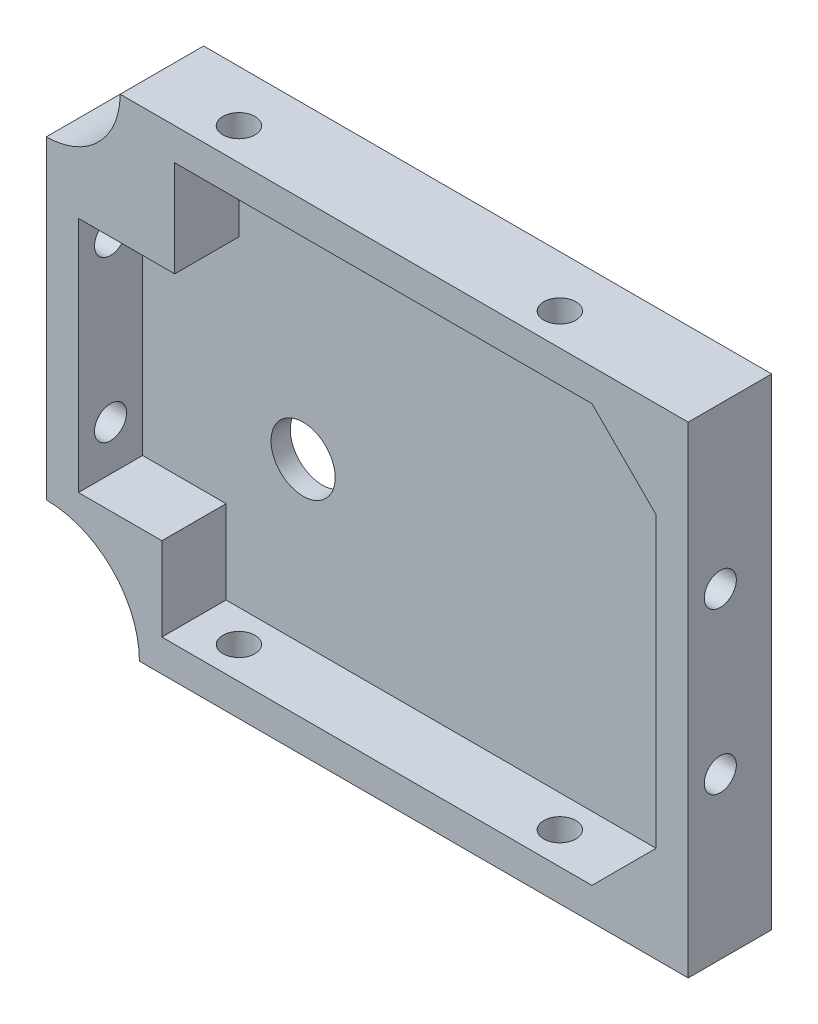
SolidWorks part; units mm, degrees
ref_plane "Plan de face" through (0, 0, 0) normal (0, 0, 1) x (1, 0, 0)
ref_plane "Plan de dessus" through (0, 0, 0) normal (0, 1, 0) x (1, 0, 0)
ref_plane "Plan de droite" through (0, 0, 0) normal (1, 0, 0) x (0, 0, -1)
sketch "Esquisse1" plane through (0, 0, 0) normal (0, 0, 1) x (1, 0, 0)
  line L0 (44.1184, 33.7284) -> (54.1184, 33.7284)
  line L1 (-45.8816, 33.7284) -> (44.1184, 33.7284)
  line L2 (-45.8816, 33.7284) -> (-45.8816, -41.2716)
  line L3 (-45.8816, -41.2716) -> (54.1184, -41.2716)
  line L4 (54.1184, 23.7284) -> (54.1184, -41.2716)
  line L5 (54.1184, 33.7284) -> (54.1184, 23.7284)
  point P6 (54.1184, 33.7284)
  dimension "D1" = 100
  dimension "D2" = 75
extrude "Boss.-Extru.1" add sketch "Esquisse1" along normal blind 13
shell "Coque1" thickness 5
sketch "Esquisse2" plane through (-45.8816, 0, 0) normal (-1, 0, 0) x (0, 0, 1)
  line L0 (13, 33.7284) -> (13, -41.2716) construction
  line L1 (13, 33.7284) -> (0, 33.7284) construction
  line L2 (13, -41.2716) -> (0, -41.2716) construction
  circle A0 centre (8, 8.7284) radius 2.5
  circle A1 centre (8, -16.2716) radius 2.5
  dimension "D1" = 5
  dimension "D2" = 5
  dimension "D3" = 5
  dimension "D4" = 5
  dimension "D5" = 25
  dimension "D6" = 25
extrude "Enlèv. mat.-Extru.1" cut sketch "Esquisse2" against normal up to surface (100 mm away) contours A1 | A0 up to face at (54.1184, -3.7716, 6.5)
sketch "Esquisse3" plane through (0, -41.2716, 0) normal (0, -1, 0) x (1, 0, 0)
  line L0 (-45.8816, 13) -> (54.1184, 13) construction
  line L2 (54.1184, 13) -> (54.1184, 0) construction
  line L3 (-45.8816, 13) -> (-45.8816, 0) construction
  circle A0 centre (-20.8816, 8) radius 2.5
  circle A1 centre (29.1184, 8) radius 2.5
  dimension "D1" = 5
  dimension "D2" = 5
  dimension "D3" = 5
  dimension "D4" = 5
  dimension "D5" = 25
  dimension "D6" = 25
extrude "Enlèv. mat.-Extru.2" cut sketch "Esquisse3" against normal up to surface (75 mm away) up to face at (4.1184, 33.7284, 6.5)
sketch "Esquisse4" plane through (0, 0, 3) normal (0, 0, 1) x (1, 0, 0)
  line L1 (49.1184, 28.7284) -> (-40.8816, 28.7284) construction
  line L2 (-45.8816, -41.2716) -> (-27.8816, -41.2716)
  line L3 (-40.8816, 28.7284) -> (-40.8816, -36.2716) construction
  line L4 (-45.8816, -41.2716) -> (-45.8816, -23.2716)
  line L5 (49.1184, 28.7284) -> (49.1184, 18.7284)
  line L6 (49.1184, -36.2716) -> (49.1184, 28.7284) construction
  line L7 (49.1184, 18.7284) -> (39.1184, 28.7284)
  line L8 (39.1184, 28.7284) -> (49.1184, 28.7284)
  line L9 (49.1184, 28.7284) -> (-40.8816, 28.7284) construction
  line L10 (49.1184, -36.2716) -> (49.1184, -26.2716)
  line L11 (49.1184, -26.2716) -> (39.1184, -36.2716)
  line L12 (-40.8816, -36.2716) -> (49.1184, -36.2716) construction
  line L13 (39.1184, -36.2716) -> (49.1184, -36.2716)
  line L14 (-40.8816, 28.7284) -> (-40.8816, -36.2716) construction
  line L15 (-45.8816, -23.2716) -> (-27.8816, -23.2716)
  line L16 (-27.8816, -41.2716) -> (-27.8816, -23.2716)
  line L17 (-25.8816, 28.7284) -> (-25.8816, 13.7284)
  line L18 (-25.8816, 13.7284) -> (-40.8816, 13.7284)
  line L19 (-40.8816, 13.7284) -> (-40.8816, 28.7284)
  line L20 (-40.8816, 28.7284) -> (-25.8816, 28.7284)
  dimension "D1" = 18
  dimension "D2" = 18
  dimension "D3" = 10
  dimension "D4" = 10
  dimension "D5" = 10
  dimension "D6" = 10
  dimension "D7" = 15
  dimension "D8" = 15
extrude "Boss.-Extru.2" add sketch "Esquisse4" along normal up to surface (10 mm away) up to face at (4.1184, -3.7716, 13)
sketch "Esquisse6" plane through (0, 0, 13) normal (0, 0, 1) x (1, 0, 0)
  circle A0 centre (-45.8816, 33.7284) radius 11.5
  circle A1 centre (-45.8816, -41.2716) radius 14.5
  dimension "D1" = 23
  dimension "D2" = 29
extrude "Enlèv. mat.-Extru.4" cut sketch "Esquisse6" against normal up to surface (13 mm away) up to face at (4.1184, -3.7716, 0)
sketch "Esquisse7" plane through (0, 0, 3) normal (0, 0, 1) x (1, 0, 0)
  line L3 (-31.3816, -41.2716) -> (54.1184, -41.2716) construction
  line L4 (-45.8816, 22.2284) -> (-45.8816, -26.7716) construction
  circle A0 centre (-15.8816, -11.2716) radius 5
  point P6 (32.5326, 11.931)
  point P7 (49.1184, 11.2331)
  dimension "D1" = 10
  dimension "D2" = 30
  dimension "D3" = 30
extrude "Enlèv. mat.-Extru.5" cut sketch "Esquisse7" against normal up to surface (3 mm away) up to face at (-7.3174, -3.168, 0)
